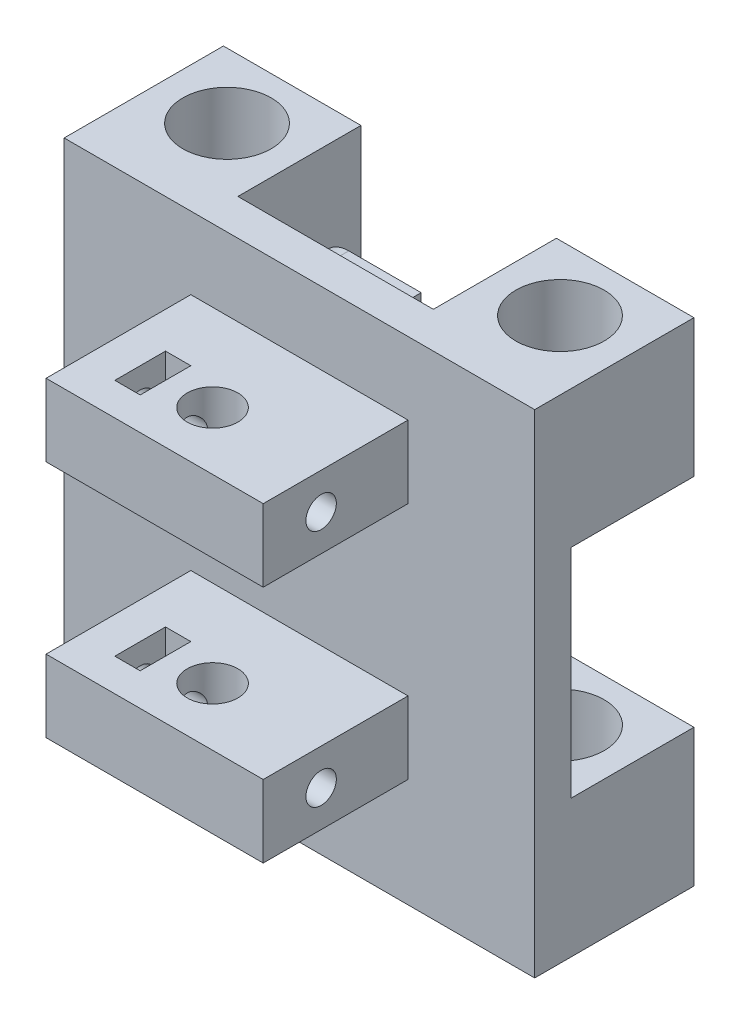
SolidWorks part; units mm, degrees
ref_plane "Front Plane" through (0, 0, 0) normal (0, 0, 1) x (1, 0, 0)
ref_plane "Top Plane" through (0, 0, 0) normal (0, 1, 0) x (1, 0, 0)
ref_plane "Right Plane" through (0, 0, 0) normal (1, 0, 0) x (0, 0, -1)
sketch "Sketch1" plane through (0, 0, 0) normal (0, 1, 0) x (1, 0, 0)
  line L0 (-23, 0) -> (23, 0) construction
  line L1 (-32.5, 9) -> (-13.5, 9)
  line L2 (-13.5, 9) -> (-13.5, -8)
  line L3 (-13.5, -8) -> (-32.5, -8)
  line L4 (-32.5, -8) -> (-32.5, 9)
  line L5 (0, 16.9538) -> (0, -28.3436) construction
  line L6 (13.5, 9) -> (13.5, -8)
  line L7 (32.5, 9) -> (13.5, 9)
  line L8 (32.5, -8) -> (32.5, 9)
  line L9 (13.5, -8) -> (32.5, -8)
  line L10 (-32.5, -8) -> (-32.5, -13)
  line L11 (-32.5, -13) -> (32.5, -13)
  line L12 (32.5, -13) -> (32.5, -8)
  line L13 (-13.5, -8) -> (13.5, -8)
  circle A0 centre (-23, 0) radius 6.1
  circle A1 centre (23, 0) radius 6.1
  point P3 (0, 0)
  dimension "D2" = 12.2
  dimension "D3" = 12.2
  dimension "D1" = 46
  dimension "D4" = 17
  dimension "D5" = 19
  dimension "D6" = 9.5
  dimension "D7" = 8
  dimension "D8" = 5
extrude "Boss-Extrude1" add sketch "Sketch1" along normal blind 68 contours L4 L3 L2 L1 A0 | L6 L9 L8 L7 A1 | L13 L3 L10 L11 L12 L9
ref_plane "Plane1" through (0, 0, -9) normal (0, 0, -1) x (-1, 0, 0)
sketch "Sketch3" plane through (0, 0, -9) normal (0, 0, -1) x (-1, 0, 0)
  line L0 (-32.5, 0) -> (-32.5, 19) construction
  line L1 (-32.5, 68) -> (-32.5, 0) construction
  line L2 (-32.5, 68) -> (-32.5, 49) construction
  line L3 (-32.5, 49) -> (32.5, 49)
  line L4 (32.5, 68) -> (32.5, 0) construction
  line L5 (-32.5, 19) -> (32.5, 19)
  line L6 (32.5, 19) -> (32.5, 49)
  line L7 (-32.5, 19) -> (-32.5, 49)
  dimension "D1" = 19
extrude "Cut-Extrude1" cut sketch "Sketch3" against normal up to surface (17 mm away) up to face at (0, 34, 8)
sketch "Sketch4" plane through (0, 0, 8) normal (0, 0, -1) x (-1, 0, 0)
  line L0 (11.2, 68) -> (11.2, 60.15) construction
  line L1 (13.5, 68) -> (-13.5, 68) construction
  line L2 (11.2, 60.15) -> (13.5, 60.15) construction
  line L3 (13.5, 68) -> (13.5, 49) construction
  line L4 (11.2, 60.15) -> (5.3, 60.15)
  line L5 (2.7063, 62.5) -> (2.7063, 57.8)
  line L7 (-6.7, 62.15) -> (2.7063, 62.5)
  line L9 (-6.7, 58.15) -> (2.7063, 57.8)
  line L11 (-8.821, 58.15) -> (-3.821, 58.15)
  line L12 (-3.821, 58.15) -> (-3.821, 54.15)
  line L13 (-3.821, 54.15) -> (-8.821, 54.15)
  line L14 (-8.821, 54.15) -> (-8.821, 58.15)
  line L16 (-8.821, 62.15) -> (1.179, 62.15)
  line L17 (1.179, 62.15) -> (1.179, 66.15)
  line L18 (1.179, 66.15) -> (-8.821, 66.15)
  line L19 (-8.821, 66.15) -> (-8.821, 62.15)
  circle A0 centre (5.3, 60.15) radius 5.9 construction
  circle A2 centre (5.3, 60.15) radius 3.5
  circle A4 centre (-6.7, 60.15) radius 2
  circle A5 centre (5.3, 60.15) radius 12 construction
  arc A6 (-2.821, 62.15) -> (1.179, 66.15) centre (1.179, 62.15) ccw
  arc A7 (1.179, 62.15) -> (4.1912, 59.5181) centre (1.3692, 59.328) cw
  dimension "D2" = 7
  dimension "D3" = 11.8
  dimension "D5" = 4.7
  dimension "D6" = 4
  dimension "D1" = 2.3
  dimension "D4" = 7.85
  dimension "D7" = 12
  dimension "D8" = 9.4063
extrude "Boss-Extrude2" add sketch "Sketch4" along normal blind 3 contours L18 L19 L16 L7 L17 | L16 L17 L7 | L14 L13 L12 L9 L11 | L12 L11 L9 | L5 A7 A6 A2 | A2 A6 L17 L7 | L17 A7 A2 L7 | A2 A7 L5
sketch "Sketch5" plane through (0, 0, 13) normal (0, 0, 1) x (1, 0, 0)
  line L0 (-15, 15) -> (15, 15)
  line L1 (-32.5, 0) -> (32.5, 0) construction
  line L2 (-3.5, -21.2953) -> (3.5, -21.2953) construction
  line L3 (0, -24.8) -> (-3.5, -21.2953) construction
  line L4 (0, -24.8) -> (3.5, -21.2953) construction
  line L5 (-3.5, -21.2953) -> (-3.5, 113.7047) construction
  line L6 (3.5, -21.2953) -> (3.5, 113.7047) construction
  line L7 (3.5, 113.7047) -> (-3.5, 113.7047) construction
  line L8 (-15, 15) -> (-15, 25)
  line L9 (-15, 25) -> (15, 25)
  line L10 (15, 25) -> (15, 15)
  line L11 (-15, 48) -> (15, 48)
  line L12 (15, 48) -> (15, 58)
  line L13 (15, 58) -> (-15, 58)
  line L14 (-15, 58) -> (-15, 48)
  line L15 (-32.5, 68) -> (32.5, 68) construction
  line L16 (0, -24.8) -> (0, 15) construction
  line L17 (0, 58) -> (0, 15) construction
  point P2 (0, 15)
  dimension "D1" = 15
  dimension "D2" = 10
  dimension "D3" = 10
  dimension "D4" = 10
extrude "Boss-Extrude3" add sketch "Sketch5" along normal blind 20
sketch "Sketch6" plane through (0, 58, 0) normal (0, 1, 0) x (1, 0, 0)
  circle A0 centre (0, -25) radius 3.5
  dimension "D1" = 7
extrude "Cut-Extrude2" cut sketch "Sketch6" against normal through all
ref_plane "Plane2" through (-15, 0, 0) normal (-1, 0, 0) x (0, 0, 1)
sketch "Sketch8" plane through (-15, 0, 0) normal (-1, 0, 0) x (0, 0, 1)
  circle A0 centre (25, 20) radius 2.1
  circle A1 centre (25, 53) radius 2.1
  dimension "D1" = 4.2
  dimension "D2" = 4.2
extrude "Cut-Extrude3" cut sketch "Sketch8" against normal through all
sketch "Sketch9" plane through (0, 15, 0) normal (0, -1, 0) x (1, 0, 0)
  line L0 (0, 25) -> (-15, 25) construction
  line L1 (-15, 12.4158) -> (-15, -12.4158) construction
  line L2 (-15, 25) -> (-10, 25)
  line L3 (-10, 21.5) -> (-10, 28.5)
  line L4 (-10, 21.5) -> (-6.5, 21.5)
  line L5 (-6.5, 21.5) -> (-6.5, 28.5)
  line L6 (-6.5, 28.5) -> (-10, 28.5)
  dimension "D1" = 5
  dimension "D2" = 7
  dimension "D3" = 3.5
extrude "Cut-Extrude4" cut sketch "Sketch9" against normal up to surface (43 mm away) contours L5 L0 L3 L4 | L0 L5 L6 L3 up to face at (0, 58, 28.5)
